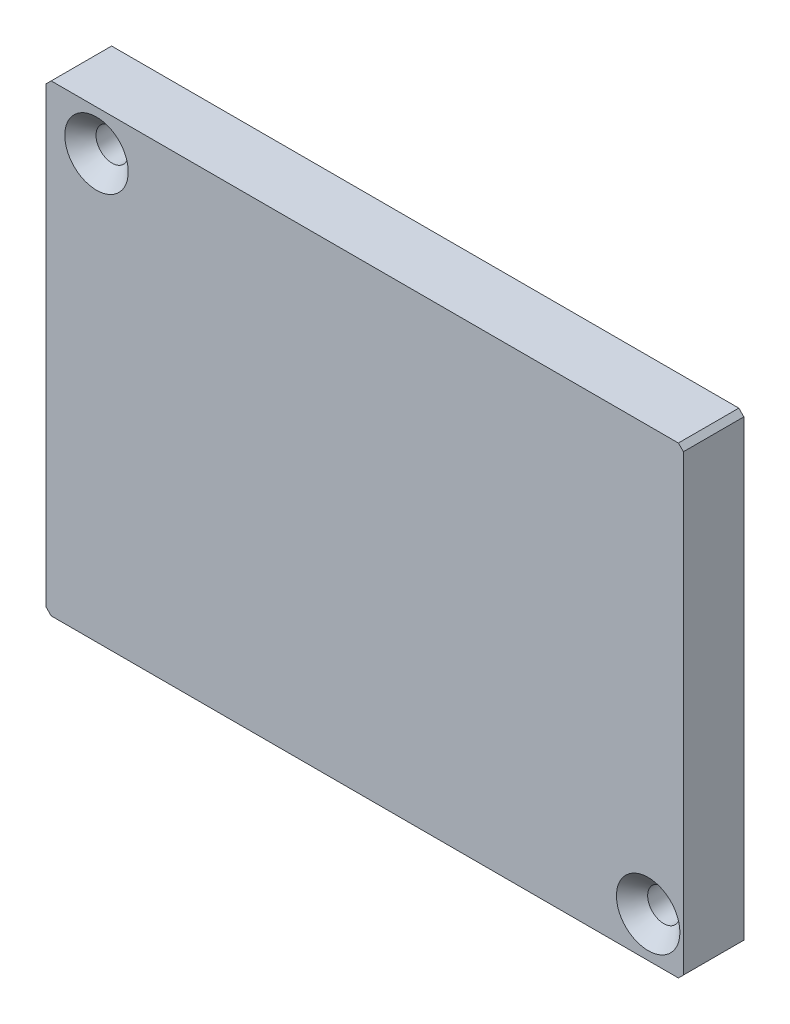
SolidWorks part; units mm, degrees
material "3.1645 (EN-AW 2030)"
ref_plane "Přední rovina" through (0, 0, 0) normal (0, 0, 1) x (1, 0, 0)
ref_plane "Horní rovina" through (0, 0, 0) normal (0, 1, 0) x (1, 0, 0)
ref_plane "Pravá rovina" through (0, 0, 0) normal (1, 0, 0) x (0, 0, -1)
sketch "Skica1" plane through (0, 0, 0) normal (0, 0, 1) x (1, 0, 0)
  line L20 (-326.8797, 22.5) -> (-326.8797, -22.5)
  line L21 (-326.8797, -22.5) -> (-326.3797, -23)
  line L22 (-326.3797, -23) -> (-264.1099, -23)
  line L23 (-264.1099, -23) -> (-263.6099, -22.5)
  line L24 (-263.6099, -22.5) -> (-263.6099, 22.5)
  line L25 (-263.6099, 22.5) -> (-264.1099, 23)
  line L26 (-264.1099, 23) -> (-326.3797, 23)
  line L27 (-326.3797, 23) -> (-326.8797, 22.5)
  line L28 (-326.8797, 22.5) -> (-326.8797, -22.5)
  line L29 (-326.8797, -22.5) -> (-326.3797, -23)
  line L30 (-326.3797, -23) -> (-264.1099, -23)
  line L31 (-264.1099, -23) -> (-263.6099, -22.5)
  line L32 (-263.6099, -22.5) -> (-263.6099, 22.5)
  line L33 (-263.6099, 22.5) -> (-264.1099, 23)
  line L34 (-264.1099, 23) -> (-326.3797, 23)
  line L35 (-326.3797, 23) -> (-326.8797, 22.5)
  circle A0 centre (-276.6099, 8.8875) radius 2.25 construction
  circle A1 centre (-298.6099, -13.1125) radius 2.25 construction
  circle A6 centre (-276.6099, 8.8875) radius 2.25 construction
  circle A7 centre (-298.6099, -13.1125) radius 2.25 construction
  circle A8 centre (-298.6099, -13.1125) radius 3.25 construction
  circle A9 centre (-276.6099, 8.8875) radius 3.25 construction
  circle A10 centre (-267.1099, 19) radius 3.1 construction
  circle A11 centre (-267.1099, 19) radius 3.1 construction
  circle A12 centre (-321.8797, -19) radius 3.1 construction
  circle A13 centre (-321.8797, -19) radius 3.1 construction
  dimension "D1" = 0
  dimension "D2" = 1
extrude "Přidat vysunutím2" add sketch "Skica1" along normal blind 6
hole_wizard "Ø6.3 (6.3) průměr díry1" positions "3DSkica1" profile "Skica2" hole size "Ø6.3" standard "ISO"
sketch3d "3DSkica1"
  point P0 (-267.1099, 19, 0)
  point P3 (-276.6099, 8.8875, 0)
  point P6 (-298.6099, -13.1125, 0)
  point P9 (-321.8797, -19, 0)
  point P13 (-267.1099, 19, 0)
  point P15 (-276.6099, 8.8875, 0)
  point P17 (-298.6099, -13.1125, 0)
  point P21 (-298.6099, -13.1125, 0)
  point P23 (-276.6099, 8.8875, 0)
  point P25 (-267.1099, 19, 0)
  point P27 (-321.8797, -19, 0)
sketch "Skica2" plane through (-321.8797, -19, 0) normal (1, 0, 0) x (0, 1, 0)
  line L0 (0, 0) -> (0, 3.8927)
  line L1 (0, 3.8927) -> (3.15, 2)
  line L2 (3.15, 2) -> (3.15, 0.05)
  line L3 (3.15, 0.05) -> (3.2, 0)
  line L5 (3.2, 0) -> (0, 0)
  line L6 (-3.15, 0.05) -> (-3.2, 0) construction
  line L10 (0, 3.8927) -> (-3.15, 2) construction
  line L11 (0, -6.35) -> (0, 107.95) construction
  dimension "Průměr díry" = 6.3
  dimension "Hloubka díry" = 2
  dimension "Průměr blíz. kuž. zahloubení" = 6.4
  dimension "Úhel blíz. kuž. zahloubení" = 90
  dimension "Úhel vrtání" = 118
hole_wizard "Kuželové zahloubení pro M3 šroubu se zápustnou hlavou plochou1" positions "3DSkica2" profile "Skica3" countersink size "M3" standard "ISO" end condition up to next
sketch3d "3DSkica2"
  point P0 (-321.8797, 19, 6)
  point P2 (-267.1099, -19, 6)
sketch "Skica3" plane through (-321.8797, 19, 6) normal (1, 0, 0) x (0, -1, 0)
  line L0 (0, 0) -> (0, 6)
  line L1 (0, 6) -> (1.6, 6)
  line L2 (1.6, 6) -> (1.6, 1.55)
  line L3 (1.6, 1.55) -> (3.15, 0)
  line L5 (3.15, 0) -> (0, 0)
  line L6 (-1.6, 1.55) -> (-3.15, 0) construction
  line L11 (0, -6.35) -> (0, 107.95) construction
  dimension "Průměr díry skrz" = 3.2
  dimension "Hloubka díry skrz" = 6
  dimension "Průměr blíz. kuž. zahloubení" = 6.3
  dimension "Úhel blíz. kuž. zahloubení" = 90
